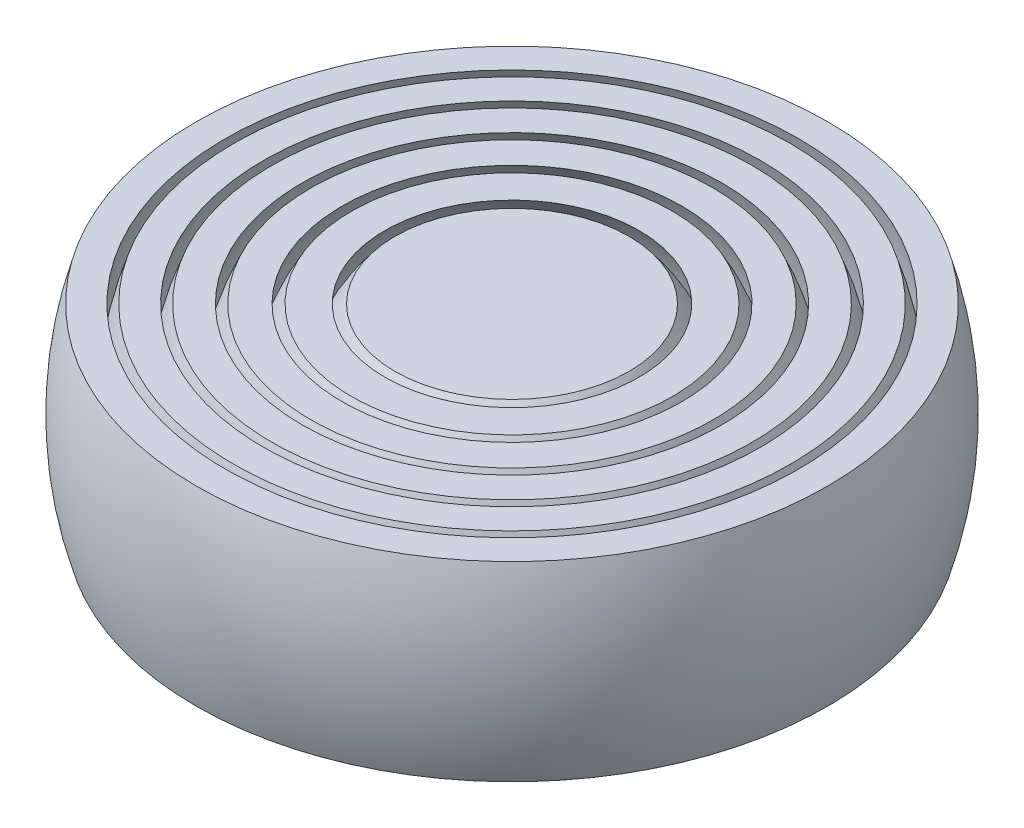
SolidWorks part; units mm, degrees
ref_plane "Front Plane" through (0, 0, 0) normal (0, 0, 1) x (1, 0, 0)
ref_plane "Top Plane" through (0, 0, 0) normal (0, 1, 0) x (1, 0, 0)
ref_plane "Right Plane" through (0, 0, 0) normal (1, 0, 0) x (0, 0, -1)
sketch "Sketch1" plane through (0, 0, 0) normal (0, 0, 1) x (1, 0, 0)
  line L0 (0, 18.5) -> (0, 16.75)
  line L1 (0, 20.75) -> (0, 19)
  line L2 (0, -19) -> (0, -20.75)
  line L3 (0, -16.75) -> (0, -18.5)
  line L4 (0, -16.75) -> (0, -18.5)
  line L5 (0, -14.5) -> (0, -16.25)
  line L6 (0, -14.5) -> (0, -16.25)
  line L7 (0, -12.25) -> (0, -14)
  line L8 (0, -12.25) -> (0, -14)
  line L9 (0, -10) -> (0, -11.75)
  line L10 (0, -10) -> (0, -11.75)
  line L11 (0, 18.5) -> (0, 16.75)
  line L12 (0, 16.25) -> (0, 14.5)
  line L13 (0, 16.25) -> (0, 14.5)
  line L14 (0, 14) -> (0, 12.25)
  line L15 (0, 14) -> (0, 12.25)
  line L16 (0, 11.75) -> (0, 10)
  line L17 (0, 11.75) -> (0, 10)
  line L18 (0, 9.5) -> (0, -9.5)
  line L19 (0, 9.5) -> (0, -9.5)
  arc A0 (0, 10) -> (0, -10) centre (0, 0) ccw
  arc A1 (0, 11.75) -> (0, -11.75) centre (0, 0) ccw
  arc A2 (0, 12.25) -> (0, -12.25) centre (0, 0) ccw
  arc A3 (0, 14) -> (0, -14) centre (0, 0) ccw
  arc A4 (0, 14.5) -> (0, -14.5) centre (0, 0) ccw
  arc A5 (0, 16.25) -> (0, -16.25) centre (0, 0) ccw
  arc A6 (0, 16.75) -> (0, -16.75) centre (0, 0) ccw
  arc A7 (0, 18.5) -> (0, -18.5) centre (0, 0) ccw
  arc A8 (0, 19) -> (0, -19) centre (0, 0) ccw
  arc A9 (0, 20.75) -> (0, -20.75) centre (0, 0) ccw
  arc A10 (0, 9.5) -> (0, -9.5) centre (0, 0) ccw
  dimension "D1" = 10
  dimension "D2" = 1.75
  dimension "D3" = 0.5
  dimension "D4" = 1.75
  dimension "D5" = 0.5
  dimension "D6" = 1.75
  dimension "D7" = 0.5
  dimension "D8" = 1.75
  dimension "D9" = 0.5
  dimension "D10" = 1.75
  dimension "D11" = 0.5
revolve "Revolve2" add sketch "Sketch1" angle 360 about L18
sketch "Sketch2" plane through (0, 0, 0) normal (0, 0, 1) x (1, 0, 0)
  line L1 (-37.4407, 30.0955) -> (36.8846, 30.0955)
  line L2 (-37.4407, 30.0955) -> (-37.4407, 6)
  line L3 (-37.4407, 6) -> (36.8846, 6)
  line L4 (36.8846, 30.0955) -> (36.8846, 6)
  line L5 (-37.4407, -6) -> (36.8846, -6)
  line L6 (-37.4407, -6) -> (-37.4407, -31.5783)
  line L7 (-37.4407, -31.5783) -> (36.8846, -31.5783)
  line L8 (36.8846, -6) -> (36.8846, -31.5783)
  dimension "D1" = 6
  dimension "D2" = 6
extrude "Cut-Extrude1" cut sketch "Sketch2" against normal through all both and the other way through all
equation "\"width\"= 1.75"
equation "\"D2@Sketch1\"=\"width\""
equation "\"gap\" = 0.5"
equation "\"D3@Sketch1\"=\"gap\""
equation "\"D4@Sketch1\"=\"width\""
equation "\"D5@Sketch1\"=\"gap\""
